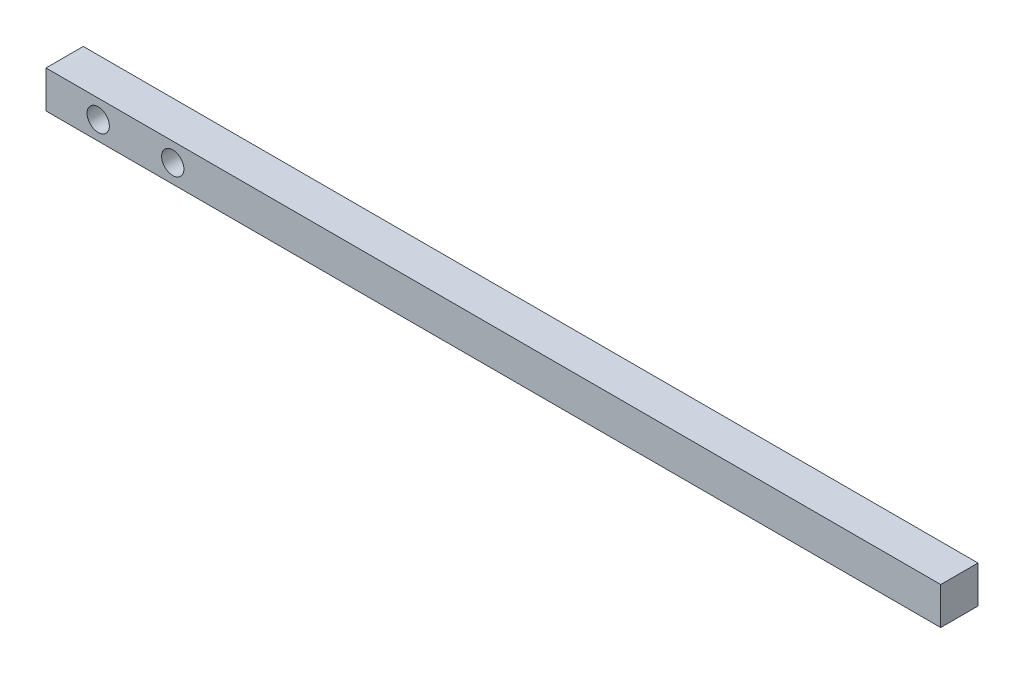
SolidWorks part; units mm, degrees
ref_plane "Front Plane" through (0, 0, 0) normal (0, 0, 1) x (1, 0, 0)
ref_plane "Top Plane" through (0, 0, 0) normal (0, 1, 0) x (1, 0, 0)
ref_plane "Right Plane" through (0, 0, 0) normal (1, 0, 0) x (0, 0, -1)
sketch "Sketch1" plane through (0, 0, 0) normal (0, 0, 1) x (1, 0, 0)
  line L1 (-76.2, -3.175) -> (76.2, -3.175)
  line L2 (-76.2, -3.175) -> (-76.2, 3.175)
  line L3 (-76.2, 3.175) -> (76.2, 3.175)
  line L4 (76.2, -3.175) -> (76.2, 3.175)
  line L5 (-76.2, -3.175) -> (76.2, 3.175) construction
  line L6 (-76.2, 3.175) -> (76.2, -3.175) construction
  point P0 (0, 0)
  dimension "D1" = 6.35
  dimension "D2" = 152.4
extrude "Boss-Extrude1" add sketch "Sketch1" along normal blind 6.35
hole_wizard "#6 Clearance Hole1" positions "Sketch3" profile "Sketch2" hole size "#6" standard "ANSI Inch" end condition through all
sketch "Sketch3" plane through (0, 0, 6.35) normal (0, 0, 1) x (1, 0, 0)
  line L0 (-76.2, 0) -> (-26.0399, 0) construction
  line L1 (-76.2, 3.175) -> (-76.2, -3.175) construction
  point P0 (-67.31, 0)
  point P2 (-54.61, 0)
  dimension "D1" = 12.7
  dimension "D2" = 8.89
sketch "Sketch2" plane through (-67.31, 0, 6.35) normal (1, 0, 0) x (0, -1, 0)
  line L0 (0, 0) -> (0, 6.35)
  line L1 (0, 6.35) -> (1.8986, 6.35)
  line L2 (1.8986, 6.35) -> (1.8986, 0)
  line L5 (1.8986, 0) -> (0, 0)
  line L11 (0, -6.35) -> (0, 107.95) construction
  dimension "Thru Hole Dia." = 3.7973
  dimension "Thru Hole Depth" = 6.35
